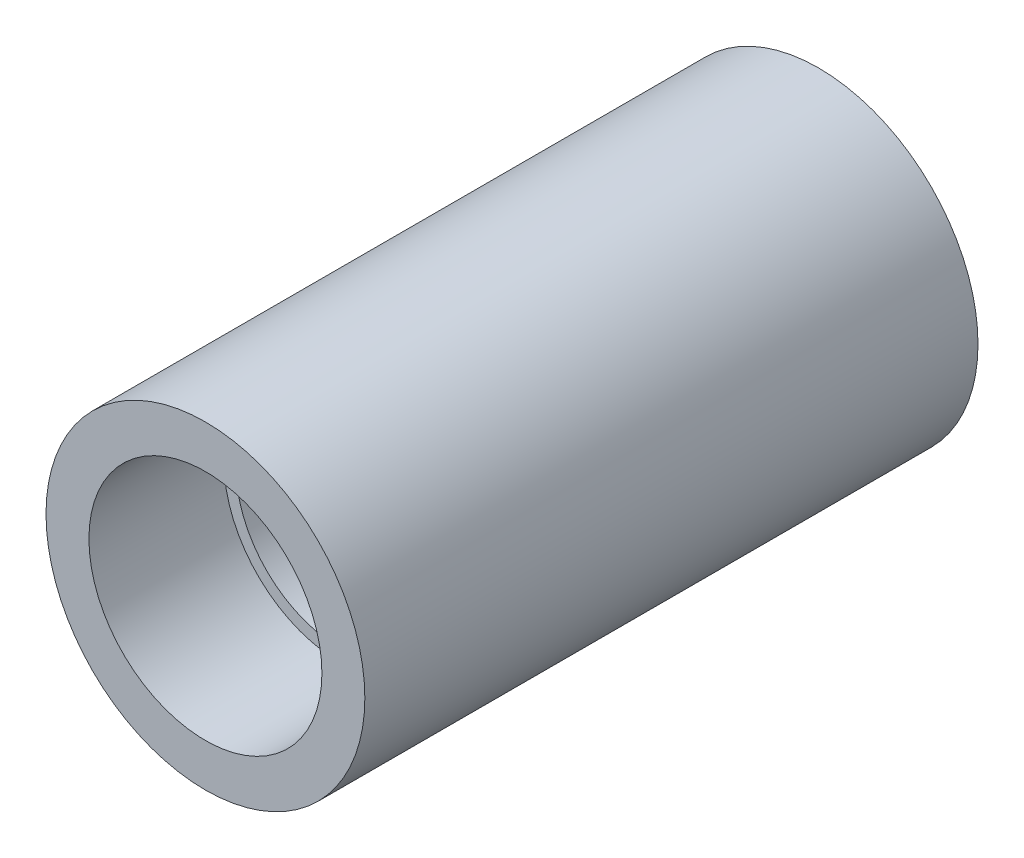
SolidWorks part; units mm, degrees
ref_plane "Front Plane" through (0, 0, 0) normal (0, 0, 1) x (1, 0, 0)
ref_plane "Top Plane" through (0, 0, 0) normal (0, 1, 0) x (1, 0, 0)
ref_plane "Right Plane" through (0, 0, 0) normal (1, 0, 0) x (0, 0, -1)
sketch "Sketch2" plane through (0, 0, 0) normal (0, 0, 1) x (1, 0, 0)
  circle A0 centre (5.6548, 0) radius 6.5
  dimension "D1" = 13
extrude "Boss-Extrude1" add sketch "Sketch2" along normal blind 25
sketch "Sketch3" plane through (0, 0, 25) normal (0, 0, 1) x (1, 0, 0)
  circle A0 centre (5.6548, 0) radius 4.75
  dimension "D1" = 9.5
extrude "Cut-Extrude1" cut sketch "Sketch3" against normal blind 5.5
sketch "Sketch4" plane through (0, 0, 19.5) normal (0, 0, 1) x (1, 0, 0)
  circle A0 centre (5.6548, 0) radius 4.25
  dimension "D1" = 8.5
extrude "Cut-Extrude2" cut sketch "Sketch4" against normal blind 5
sketch "Sketch6" plane through (0, 0, 0) normal (0, 0, -1) x (-1, 0, 0)
  circle A0 centre (-5.6548, 0) radius 4.75
  dimension "D1" = 9.5
extrude "Cut-Extrude3" cut sketch "Sketch6" against normal blind 7.5
sketch "Sketch7" plane through (0, 0, 14.5) normal (0, 0, 1) x (1, 0, 0)
  circle A0 centre (5.6548, 0) radius 2.75
  dimension "D1" = 5.5
extrude "Cut-Extrude4" cut sketch "Sketch7" against normal up to next
